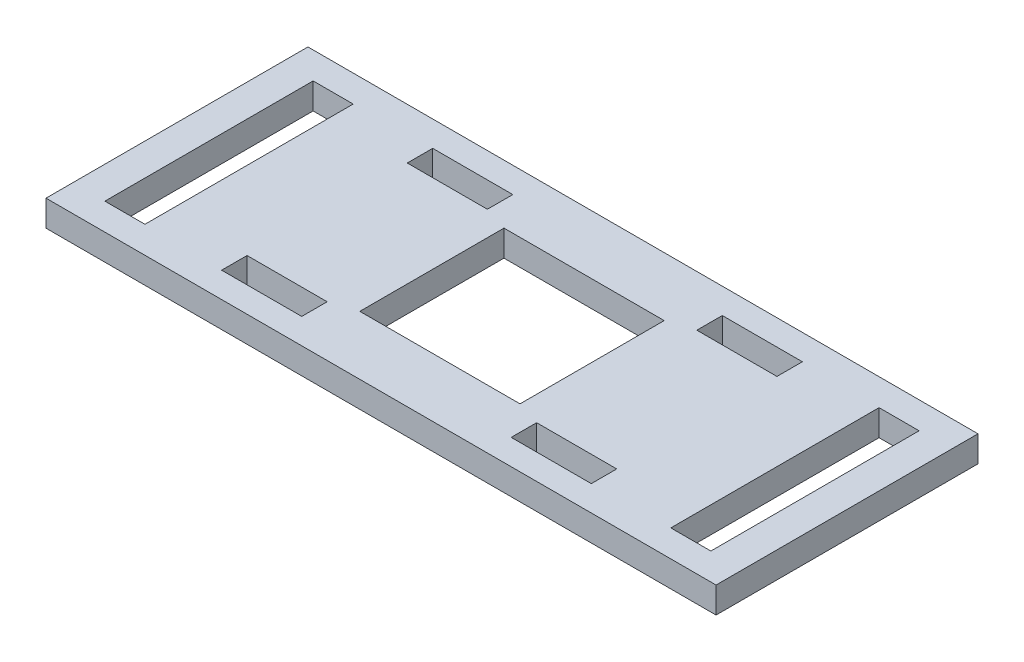
SolidWorks part; units mm, degrees
ref_plane "Front Plane" through (0, 0, 0) normal (0, 0, 1) x (1, 0, 0)
ref_plane "Top Plane" through (0, 0, 0) normal (0, 1, 0) x (1, 0, 0)
ref_plane "Right Plane" through (0, 0, 0) normal (1, 0, 0) x (0, 0, -1)
sketch "Sketch1" plane through (0, 0, 0) normal (0, 1, 0) x (1, 0, 0)
  line L0 (-41.825, 13.175) -> (41.825, 13.175) construction
  line L1 (-41.825, -16.35) -> (41.825, -16.35)
  line L2 (-41.825, -16.35) -> (-41.825, 16.35)
  line L3 (-41.825, 16.35) -> (41.825, 16.35)
  line L4 (41.825, -16.35) -> (41.825, 16.35)
  line L5 (-41.825, -16.35) -> (41.825, 16.35) construction
  line L6 (-41.825, 16.35) -> (41.825, -16.35) construction
  line L7 (-41.825, 10) -> (41.825, 10) construction
  line L8 (-41.825, -13.175) -> (41.825, -13.175) construction
  line L9 (-41.825, -10) -> (41.825, -10) construction
  line L10 (-31.825, -16.35) -> (-31.825, 16.35) construction
  line L11 (-4.325, -16.35) -> (-4.325, 16.35) construction
  line L12 (31.825, -16.35) -> (31.825, 16.35) construction
  line L13 (0, 16.35) -> (0, -16.35) construction
  line L14 (-31.825, 0) -> (-4.325, 0) construction
  line L15 (-37.825, -13) -> (-32.825, -13)
  line L16 (-37.825, -13) -> (-37.825, 13)
  line L17 (-37.825, 13) -> (-32.825, 13)
  line L18 (-32.825, -13) -> (-32.825, 13)
  line L19 (-37.825, -13) -> (-32.825, 13) construction
  line L20 (-37.825, 13) -> (-32.825, -13) construction
  line L21 (-18.075, 0) -> (-18.075, 10) construction
  line L22 (37.825, 13) -> (32.825, -13) construction
  line L23 (-23.075, 10) -> (-13.075, 10)
  line L24 (-23.075, 10) -> (-23.075, 13.175)
  line L25 (-23.075, 13.175) -> (-13.075, 13.175)
  line L26 (-13.075, 10) -> (-13.075, 13.175)
  line L27 (37.825, -13) -> (32.825, 13) construction
  line L28 (32.825, -13) -> (32.825, 13)
  line L29 (37.825, 13) -> (32.825, 13)
  line L30 (37.825, -13) -> (37.825, 13)
  line L31 (37.825, -13) -> (32.825, -13)
  line L32 (13.075, 10) -> (13.075, 13.175)
  line L33 (23.075, 13.175) -> (13.075, 13.175)
  line L34 (23.075, 10) -> (23.075, 13.175)
  line L35 (23.075, 10) -> (13.075, 10)
  line L36 (23.075, -10) -> (13.075, -10)
  line L37 (23.075, -10) -> (23.075, -13.175)
  line L38 (23.075, -13.175) -> (13.075, -13.175)
  line L39 (13.075, -10) -> (13.075, -13.175)
  line L40 (-13.075, -10) -> (-13.075, -13.175)
  line L41 (-23.075, -13.175) -> (-13.075, -13.175)
  line L42 (-23.075, -10) -> (-23.075, -13.175)
  line L43 (-23.075, -10) -> (-13.075, -10)
  line L45 (-10, -9) -> (10, -9)
  line L46 (-10, -9) -> (-10, 9)
  line L47 (-10, 9) -> (10, 9)
  line L48 (10, -9) -> (10, 9)
  line L49 (-10, -9) -> (10, 9) construction
  line L50 (-10, 9) -> (10, -9) construction
  point P0 (0, 0)
  point P22 (-35.325, 0)
  point P35 (-18.075, 10)
  point P40 (35.325, 0)
  point P53 (0, 0)
  dimension "D1" = 83.65
  dimension "D2" = 32.7
  dimension "D10" = 26
  dimension "D11" = 5
  dimension "D12" = 4
  dimension "D13" = 10
  dimension "D14" = 20
  dimension "D15" = 18
  dimension "D3" = 3.175
  dimension "D4" = 3.175
  dimension "D5" = 3.175
  dimension "D6" = 3.175
  dimension "D7" = 10
  dimension "D8" = 27.5
  dimension "D9" = 10
extrude "Boss-Extrude1" add sketch "Sketch1" along normal blind 3.25
